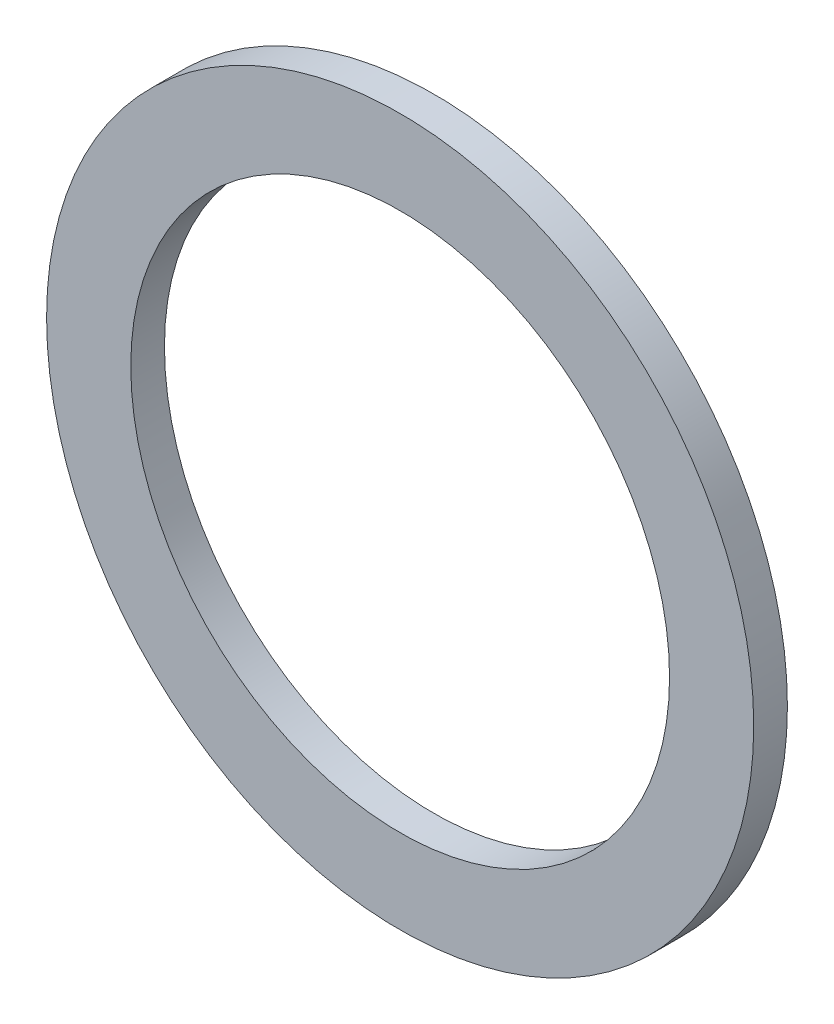
SolidWorks part; units mm, degrees
material "Alliage 7079"
ref_plane "Face" through (0, 0, 0) normal (0, 0, 1) x (1, 0, 0)
ref_plane "Dessus" through (0, 0, 0) normal (0, 1, 0) x (1, 0, 0)
ref_plane "Droite" through (0, 0, 0) normal (1, 0, 0) x (0, 0, -1)
sketch "Esquisse1" plane through (0, 0, 0) normal (0, 0, 1) x (1, 0, 0)
  circle A0 centre (0, 0) radius 8
  circle A1 centre (0, 0) radius 10.5
  dimension "D1" = 16
  dimension "D2" = 21
extrude "Extrusion1" add sketch "Esquisse1" along normal mid plane 1
